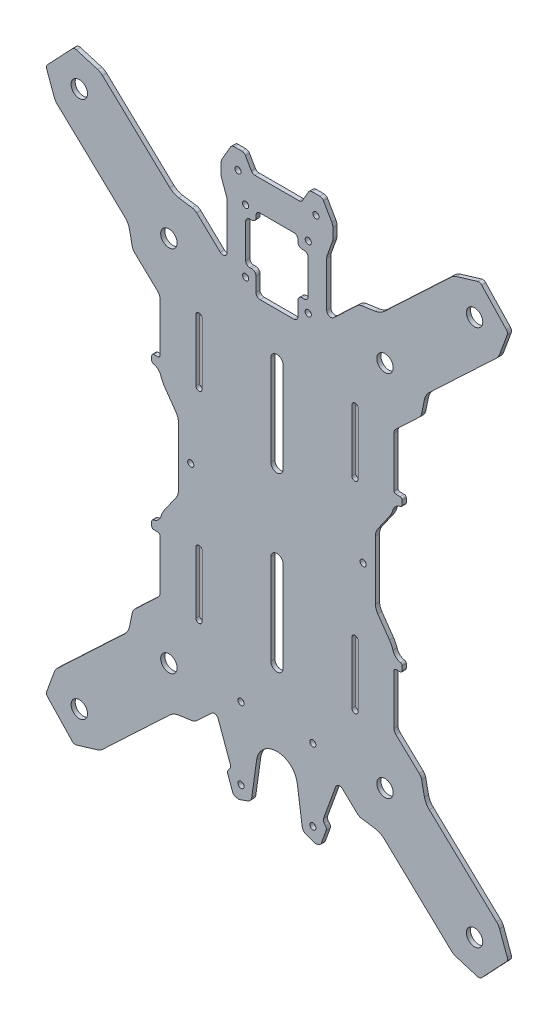
SolidWorks part; units mm, degrees
ref_plane "Front Plane" through (0, 0, 0) normal (0, 0, 1) x (1, 0, 0)
ref_plane "Top Plane" through (0, 0, 0) normal (0, 1, 0) x (1, 0, 0)
ref_plane "Right Plane" through (0, 0, 0) normal (1, 0, 0) x (0, 0, -1)
sketch "Model" plane through (0, 0, 0) normal (0, 0, 1) x (1, 0, 0)
  line L0 (200.4127, 281.3131) -> (207.0194, 282.2803)
  line L1 (211.3501, 284.3765) -> (244.1291, 315.2966)
  line L2 (246.5156, 316.677) -> (256.8221, 319.7815)
  line L3 (270.8811, 306.4885) -> (258.8538, 319.2389)
  line L4 (271.3043, 304.4286) -> (267.604, 294.3207)
  line L5 (266.0868, 292.0187) -> (233.3078, 261.0987)
  line L6 (230.9627, 256.8976) -> (229.6119, 250.3586)
  line L7 (228.4393, 248.258) -> (217.0717, 237.5351)
  line L8 (216.1302, 211.086) -> (216.1302, 235.3528)
  line L9 (219.1302, 210.086) -> (217.1302, 210.086)
  line L10 (220.1302, 206.9971) -> (220.1302, 209.086)
  line L11 (213.96, 199.2031) -> (208.2153, 190.9987)
  line L12 (207.1302, 158.6884) -> (207.1302, 187.5573)
  line L13 (208.2153, 155.2469) -> (213.96, 147.0426)
  line L14 (220.1302, 137.1597) -> (220.1302, 139.2486)
  line L15 (217.1302, 136.1597) -> (219.1302, 136.1597)
  line L16 (216.1302, 110.8929) -> (216.1302, 135.1597)
  line L17 (217.0717, 108.7106) -> (228.4393, 97.9876)
  line L18 (229.6119, 95.8871) -> (230.9627, 89.3481)
  line L19 (233.3078, 85.147) -> (266.0868, 54.2269)
  line L20 (267.604, 51.9249) -> (271.3043, 41.817)
  line L21 (258.8538, 27.0068) -> (270.8811, 39.7571)
  line L22 (256.8221, 26.4641) -> (246.5156, 29.5687)
  line L23 (244.1291, 30.9491) -> (211.3501, 61.8692)
  line L24 (207.0194, 63.9653) -> (200.4127, 64.9325)
  line L25 (198.2474, 65.9806) -> (191.0122, 72.8055)
  line L26 (181.8313, 55.7445) -> (187.7604, 72.0347)
  line L27 (182.1786, 53.7749) -> (182.7352, 53.1115)
  line L28 (183.0825, 51.1419) -> (180.7129, 44.6315)
  line L29 (179.1809, 43.3459) -> (177.8615, 43.1133)
  line L30 (177.3458, 43.1584) -> (173.3678, 44.6063)
  line L31 (171.423, 47.0078) -> (169.0329, 64.0146)
  line L32 (149.2275, 64.0146) -> (146.8374, 47.0078)
  line L33 (144.8926, 44.6063) -> (140.9146, 43.1584)
  line L34 (139.0795, 43.3459) -> (140.3989, 43.1133)
  line L35 (135.1779, 51.1419) -> (137.5474, 44.6315)
  line L36 (136.0818, 53.7749) -> (135.5252, 53.1115)
  line L37 (130.5, 72.0347) -> (136.4291, 55.7445)
  line L38 (120.013, 65.9806) -> (127.2482, 72.8055)
  line L39 (111.241, 63.9653) -> (117.8476, 64.9325)
  line L40 (74.1313, 30.9491) -> (106.9103, 61.8692)
  line L41 (61.4383, 26.4641) -> (71.7448, 29.5687)
  line L42 (47.3793, 39.7571) -> (59.4066, 27.0068)
  line L43 (50.6563, 51.9249) -> (46.9561, 41.817)
  line L44 (84.9526, 85.147) -> (52.1736, 54.2269)
  line L45 (88.6485, 95.8871) -> (87.2977, 89.3481)
  line L46 (101.1887, 108.7106) -> (89.8211, 97.9876)
  line L47 (102.1302, 135.1597) -> (102.1302, 110.8929)
  line L48 (99.1302, 136.1597) -> (101.1302, 136.1597)
  line L49 (98.1302, 139.2486) -> (98.1302, 137.1597)
  line L50 (110.0451, 155.2469) -> (104.3004, 147.0426)
  line L51 (111.1302, 187.5573) -> (111.1302, 158.6884)
  line L52 (104.3004, 199.2031) -> (110.0451, 190.9987)
  line L53 (98.1302, 209.086) -> (98.1302, 206.9971)
  line L54 (101.1302, 210.086) -> (99.1302, 210.086)
  line L55 (102.1302, 235.3528) -> (102.1302, 211.086)
  line L56 (89.8211, 248.258) -> (101.1887, 237.5351)
  line L57 (87.2977, 256.8976) -> (88.6485, 250.3586)
  line L58 (52.1736, 292.0187) -> (84.9526, 261.0987)
  line L59 (46.9561, 304.4286) -> (50.6563, 294.3207)
  line L60 (59.4066, 319.2389) -> (47.3793, 306.4885)
  line L61 (71.7448, 316.677) -> (61.4383, 319.7815)
  line L62 (106.9103, 284.3765) -> (74.1313, 315.2966)
  line L63 (117.8476, 281.3131) -> (111.241, 282.2803)
  line L64 (131.5078, 269.4221) -> (120.013, 280.2651)
  line L65 (134.8802, 292.8447) -> (134.8802, 270.877)
  line L66 (132.1214, 301.1297) -> (134.639, 294.2128)
  line L67 (131.8802, 307.2589) -> (131.8802, 302.4977)
  line L68 (136.499, 316.3307) -> (132.4161, 309.2589)
  line L69 (142.0293, 317.3307) -> (138.231, 317.3307)
  line L70 (146.6481, 311.3307) -> (143.7614, 316.3307)
  line L71 (169.8802, 310.3307) -> (148.3802, 310.3307)
  line L72 (171.6122, 311.3307) -> (174.499, 316.3307)
  line L73 (176.231, 317.3307) -> (180.0293, 317.3307)
  line L74 (181.7614, 316.3307) -> (185.8443, 309.2589)
  line L75 (186.3802, 307.2589) -> (186.3802, 302.4977)
  line L76 (186.139, 301.1297) -> (183.6214, 294.2128)
  line L77 (183.3802, 292.8447) -> (183.3802, 270.877)
  line L78 (186.7526, 269.4221) -> (198.2474, 280.2651)
  line L79 (119.6302, 109.1228) -> (119.6302, 139.1228)
  line L80 (122.6302, 139.1228) -> (122.6302, 109.1228)
  line L81 (198.6302, 237.1228) -> (198.6302, 207.1228)
  line L82 (195.6302, 207.1228) -> (195.6302, 237.1228)
  line L83 (146.8802, 270.1228) -> (145.8802, 270.1228)
  line L84 (148.8802, 261.1228) -> (148.8802, 268.1228)
  line L85 (167.3802, 259.1228) -> (150.8802, 259.1228)
  line L86 (169.3802, 268.1228) -> (169.3802, 261.1228)
  line L87 (172.3802, 270.1228) -> (171.3802, 270.1228)
  line L88 (174.3802, 288.6228) -> (174.3802, 272.1228)
  line L89 (171.3802, 290.6228) -> (172.3802, 290.6228)
  line L90 (169.3802, 293.6228) -> (169.3802, 292.6228)
  line L91 (150.8802, 295.6228) -> (167.3802, 295.6228)
  line L92 (148.8802, 292.6228) -> (148.8802, 293.6228)
  line L93 (145.8802, 290.6228) -> (146.8802, 290.6228)
  line L94 (143.8802, 272.1228) -> (143.8802, 288.6228)
  line L95 (162.1302, 237.1228) -> (162.1302, 193.1228)
  line L96 (156.1302, 193.1228) -> (156.1302, 237.1228)
  line L97 (156.1302, 109.1228) -> (156.1302, 153.1228)
  line L98 (162.1302, 153.1228) -> (162.1302, 109.1228)
  line L99 (122.6302, 237.1228) -> (122.6302, 207.1228)
  line L100 (119.6302, 207.1228) -> (119.6302, 237.1228)
  line L101 (195.6302, 109.1228) -> (195.6302, 139.1228)
  line L102 (198.6302, 139.1228) -> (198.6302, 109.1228)
  arc A0 (200.4127, 281.3131) -> (198.2474, 280.2651) centre (200.9921, 277.3553) ccw
  arc A1 (207.0194, 282.2803) -> (211.3501, 284.3765) centre (205.8606, 290.1959) ccw
  arc A2 (246.5156, 316.677) -> (244.1291, 315.2966) centre (248.2461, 310.932) ccw
  arc A3 (258.8538, 319.2389) -> (256.8221, 319.7815) centre (257.399, 317.8665) ccw
  arc A4 (271.3043, 304.4286) -> (270.8811, 306.4885) centre (269.4262, 305.1162) ccw
  arc A5 (266.0868, 292.0187) -> (267.604, 294.3207) centre (261.9697, 296.3833) ccw
  arc A6 (233.3078, 261.0987) -> (230.9627, 256.8976) centre (238.7973, 255.2792) ccw
  arc A7 (228.4393, 248.258) -> (229.6119, 250.3586) centre (225.6946, 251.1678) ccw
  arc A8 (217.0717, 237.5351) -> (216.1302, 235.3528) centre (219.1302, 235.3528) ccw
  arc A9 (216.1302, 211.086) -> (217.1302, 210.086) centre (217.1302, 211.086) ccw
  arc A10 (220.1302, 209.086) -> (219.1302, 210.086) centre (219.1302, 209.086) ccw
  arc A11 (219.3067, 206.0128) -> (220.1302, 206.9971) centre (219.1302, 206.9971) ccw
  arc A12 (219.3067, 206.0128) -> (215.6502, 202.726) centre (220.1302, 201.4193) ccw
  arc A13 (213.96, 199.2031) -> (215.6502, 202.726) centre (204.1302, 206.086) ccw
  arc A14 (208.2153, 190.9987) -> (207.1302, 187.5573) centre (213.1302, 187.5573) ccw
  arc A15 (207.1302, 158.6884) -> (208.2153, 155.2469) centre (213.1302, 158.6884) ccw
  arc A16 (215.6502, 143.5197) -> (213.96, 147.0426) centre (204.1302, 140.1597) ccw
  arc A17 (215.6502, 143.5197) -> (219.3067, 140.2329) centre (220.1302, 144.8263) ccw
  arc A18 (220.1302, 139.2486) -> (219.3067, 140.2329) centre (219.1302, 139.2486) ccw
  arc A19 (219.1302, 136.1597) -> (220.1302, 137.1597) centre (219.1302, 137.1597) ccw
  arc A20 (217.1302, 136.1597) -> (216.1302, 135.1597) centre (217.1302, 135.1597) ccw
  arc A21 (216.1302, 110.8929) -> (217.0717, 108.7106) centre (219.1302, 110.8929) ccw
  arc A22 (229.6119, 95.8871) -> (228.4393, 97.9876) centre (225.6946, 95.0779) ccw
  arc A23 (230.9627, 89.3481) -> (233.3078, 85.147) centre (238.7973, 90.9665) ccw
  arc A24 (267.604, 51.9249) -> (266.0868, 54.2269) centre (261.9697, 49.8623) ccw
  arc A25 (270.8811, 39.7571) -> (271.3043, 41.817) centre (269.4262, 41.1295) ccw
  arc A26 (256.8221, 26.4641) -> (258.8538, 27.0068) centre (257.399, 28.3791) ccw
  arc A27 (244.1291, 30.9491) -> (246.5156, 29.5687) centre (248.2461, 35.3137) ccw
  arc A28 (211.3501, 61.8692) -> (207.0194, 63.9653) centre (205.8606, 56.0497) ccw
  arc A29 (198.2474, 65.9806) -> (200.4127, 64.9325) centre (200.9921, 68.8903) ccw
  arc A30 (191.0122, 72.8055) -> (187.7604, 72.0347) centre (189.6398, 71.3507) ccw
  arc A31 (181.8313, 55.7445) -> (182.1786, 53.7749) centre (183.7106, 55.0605) ccw
  arc A32 (183.0825, 51.1419) -> (182.7352, 53.1115) centre (181.2031, 51.8259) ccw
  arc A33 (179.1809, 43.3459) -> (180.7129, 44.6315) centre (178.8336, 45.3155) ccw
  arc A34 (177.3458, 43.1584) -> (177.8615, 43.1133) centre (177.6878, 44.0981) ccw
  arc A35 (171.423, 47.0078) -> (173.3678, 44.6063) centre (174.3938, 47.4253) ccw
  arc A36 (169.0329, 64.0146) -> (149.2275, 64.0146) centre (159.1302, 62.6228) ccw
  arc A37 (144.8926, 44.6063) -> (146.8374, 47.0078) centre (143.8666, 47.4253) ccw
  arc A38 (140.3989, 43.1133) -> (140.9146, 43.1584) centre (140.5726, 44.0981) ccw
  arc A39 (137.5474, 44.6315) -> (139.0795, 43.3459) centre (139.4268, 45.3155) ccw
  arc A40 (135.5252, 53.1115) -> (135.1779, 51.1419) centre (137.0572, 51.8259) ccw
  arc A41 (136.0818, 53.7749) -> (136.4291, 55.7445) centre (134.5497, 55.0605) ccw
  arc A42 (130.5, 72.0347) -> (127.2482, 72.8055) centre (128.6206, 71.3507) ccw
  arc A43 (117.8476, 64.9325) -> (120.013, 65.9806) centre (117.2683, 68.8903) ccw
  arc A44 (111.241, 63.9653) -> (106.9103, 61.8692) centre (112.3997, 56.0497) ccw
  arc A45 (71.7448, 29.5687) -> (74.1313, 30.9491) centre (70.0143, 35.3137) ccw
  arc A46 (59.4066, 27.0068) -> (61.4383, 26.4641) centre (60.8614, 28.3791) ccw
  arc A47 (46.9561, 41.817) -> (47.3793, 39.7571) centre (48.8342, 41.1295) ccw
  arc A48 (52.1736, 54.2269) -> (50.6563, 51.9249) centre (56.2907, 49.8623) ccw
  arc A49 (84.9526, 85.147) -> (87.2977, 89.3481) centre (79.4631, 90.9665) ccw
  arc A50 (89.8211, 97.9876) -> (88.6485, 95.8871) centre (92.5658, 95.0779) ccw
  arc A51 (101.1887, 108.7106) -> (102.1302, 110.8929) centre (99.1302, 110.8929) ccw
  arc A52 (102.1302, 135.1597) -> (101.1302, 136.1597) centre (101.1302, 135.1597) ccw
  arc A53 (98.1302, 137.1597) -> (99.1302, 136.1597) centre (99.1302, 137.1597) ccw
  arc A54 (98.9537, 140.2329) -> (98.1302, 139.2486) centre (99.1302, 139.2486) ccw
  arc A55 (98.9537, 140.2329) -> (102.6102, 143.5197) centre (98.1302, 144.8263) ccw
  arc A56 (104.3004, 147.0426) -> (102.6102, 143.5197) centre (114.1302, 140.1597) ccw
  arc A57 (110.0451, 155.2469) -> (111.1302, 158.6884) centre (105.1302, 158.6884) ccw
  arc A58 (111.1302, 187.5573) -> (110.0451, 190.9987) centre (105.1302, 187.5573) ccw
  arc A59 (102.6102, 202.726) -> (104.3004, 199.2031) centre (114.1302, 206.086) ccw
  arc A60 (102.6102, 202.726) -> (98.9537, 206.0128) centre (98.1302, 201.4193) ccw
  arc A61 (98.1302, 206.9971) -> (98.9537, 206.0128) centre (99.1302, 206.9971) ccw
  arc A62 (99.1302, 210.086) -> (98.1302, 209.086) centre (99.1302, 209.086) ccw
  arc A63 (101.1302, 210.086) -> (102.1302, 211.086) centre (101.1302, 211.086) ccw
  arc A64 (102.1302, 235.3528) -> (101.1887, 237.5351) centre (99.1302, 235.3528) ccw
  arc A65 (88.6485, 250.3586) -> (89.8211, 248.258) centre (92.5658, 251.1678) ccw
  arc A66 (87.2977, 256.8976) -> (84.9526, 261.0987) centre (79.4631, 255.2792) ccw
  arc A67 (50.6563, 294.3207) -> (52.1736, 292.0187) centre (56.2907, 296.3833) ccw
  arc A68 (47.3793, 306.4885) -> (46.9561, 304.4286) centre (48.8342, 305.1162) ccw
  arc A69 (61.4383, 319.7815) -> (59.4066, 319.2389) centre (60.8614, 317.8665) ccw
  arc A70 (74.1313, 315.2966) -> (71.7448, 316.677) centre (70.0143, 310.932) ccw
  arc A71 (106.9103, 284.3765) -> (111.241, 282.2803) centre (112.3997, 290.1959) ccw
  arc A72 (120.013, 280.2651) -> (117.8476, 281.3131) centre (117.2683, 277.3553) ccw
  arc A73 (131.5078, 269.4221) -> (134.8802, 270.877) centre (132.8802, 270.8769) ccw
  arc A74 (134.8802, 292.8447) -> (134.639, 294.2128) centre (130.8802, 292.8447) ccw
  arc A75 (131.8802, 302.4977) -> (132.1214, 301.1297) centre (135.8802, 302.4977) ccw
  arc A76 (132.4161, 309.2589) -> (131.8802, 307.2589) centre (135.8802, 307.2589) ccw
  arc A77 (138.231, 317.3307) -> (136.499, 316.3307) centre (138.231, 315.3307) ccw
  arc A78 (143.7614, 316.3307) -> (142.0293, 317.3307) centre (142.0293, 315.3307) ccw
  arc A79 (146.6481, 311.3307) -> (148.3802, 310.3307) centre (148.3802, 312.3307) ccw
  arc A80 (169.8802, 310.3307) -> (171.6122, 311.3307) centre (169.8802, 312.3307) ccw
  arc A81 (176.231, 317.3307) -> (174.499, 316.3307) centre (176.231, 315.3307) ccw
  arc A82 (181.7614, 316.3307) -> (180.0293, 317.3307) centre (180.0293, 315.3307) ccw
  arc A83 (186.3802, 307.2589) -> (185.8443, 309.2589) centre (182.3802, 307.2589) ccw
  arc A84 (186.139, 301.1297) -> (186.3802, 302.4977) centre (182.3802, 302.4977) ccw
  arc A85 (183.6214, 294.2128) -> (183.3802, 292.8447) centre (187.3802, 292.8447) ccw
  arc A86 (183.3802, 270.877) -> (186.7526, 269.4221) centre (185.3802, 270.8769) ccw
  arc A87 (122.6302, 139.1228) -> (119.6302, 139.1228) centre (121.1302, 139.1228) ccw
  arc A88 (119.6302, 109.1228) -> (122.6302, 109.1228) centre (121.1302, 109.1228) ccw
  arc A89 (195.6302, 207.1228) -> (198.6302, 207.1228) centre (197.1302, 207.1228) ccw
  arc A90 (198.6302, 237.1228) -> (195.6302, 237.1228) centre (197.1302, 237.1228) ccw
  arc A91 (143.8802, 272.1228) -> (145.8802, 270.1228) centre (145.8802, 272.1228) ccw
  arc A92 (148.8802, 268.1228) -> (146.8802, 270.1228) centre (146.8802, 268.1228) ccw
  arc A93 (148.8802, 261.1228) -> (150.8802, 259.1228) centre (150.8802, 261.1228) ccw
  arc A94 (167.3802, 259.1228) -> (169.3802, 261.1228) centre (167.3802, 261.1228) ccw
  arc A95 (171.3802, 270.1228) -> (169.3802, 268.1228) centre (171.3802, 268.1228) ccw
  arc A96 (172.3802, 270.1228) -> (174.3802, 272.1228) centre (172.3802, 272.1228) ccw
  arc A97 (174.3802, 288.6228) -> (172.3802, 290.6228) centre (172.3802, 288.6228) ccw
  arc A98 (169.3802, 292.6228) -> (171.3802, 290.6228) centre (171.3802, 292.6228) ccw
  arc A99 (169.3802, 293.6228) -> (167.3802, 295.6228) centre (167.3802, 293.6228) ccw
  arc A100 (150.8802, 295.6228) -> (148.8802, 293.6228) centre (150.8802, 293.6228) ccw
  arc A101 (146.8802, 290.6228) -> (148.8802, 292.6228) centre (146.8802, 292.6228) ccw
  arc A102 (145.8802, 290.6228) -> (143.8802, 288.6228) centre (145.8802, 288.6228) ccw
  circle A103 centre (174.3802, 265.1228) radius 1.5
  circle A104 centre (143.8802, 295.6228) radius 1.5
  circle A105 centre (176.6302, 84.7678) radius 1.5
  arc A106 (156.1302, 193.1228) -> (162.1302, 193.1228) centre (159.1302, 193.1228) ccw
  arc A107 (162.1302, 237.1228) -> (156.1302, 237.1228) centre (159.1302, 237.1228) ccw
  circle A108 centre (141.6302, 49.7678) radius 1.5
  circle A109 centre (106.4955, 262.7726) radius 4
  circle A110 centre (62.8496, 303.9434) radius 4
  circle A111 centre (106.4955, 83.4731) radius 4
  circle A112 centre (62.8496, 42.3023) radius 4
  circle A113 centre (255.4108, 42.3023) radius 4
  circle A114 centre (211.7649, 83.4731) radius 4
  circle A115 centre (255.4108, 303.9434) radius 4
  circle A116 centre (211.7649, 262.7726) radius 4
  circle A117 centre (176.6302, 49.7678) radius 1.5
  arc A118 (162.1302, 153.1228) -> (156.1302, 153.1228) centre (159.1302, 153.1228) ccw
  arc A119 (156.1302, 109.1228) -> (162.1302, 109.1228) centre (159.1302, 109.1228) ccw
  circle A120 centre (141.6302, 84.7678) radius 1.5
  circle A121 centre (174.3802, 295.6228) radius 1.5
  circle A122 centre (143.8802, 265.1228) radius 1.5
  circle A123 centre (140.1302, 308.3307) radius 3.5 construction
  circle A124 centre (178.1302, 308.3307) radius 3.5 construction
  circle A125 centre (117.1302, 173.1228) radius 3.5 construction
  circle A126 centre (201.1302, 173.1228) radius 3.5 construction
  arc A127 (119.6302, 207.1228) -> (122.6302, 207.1228) centre (121.1302, 207.1228) ccw
  arc A128 (122.6302, 237.1228) -> (119.6302, 237.1228) centre (121.1302, 237.1228) ccw
  arc A129 (198.6302, 139.1228) -> (195.6302, 139.1228) centre (197.1302, 139.1228) ccw
  arc A130 (195.6302, 109.1228) -> (198.6302, 109.1228) centre (197.1302, 109.1228) ccw
  circle A131 centre (201.1302, 173.1228) radius 1.5
  circle A132 centre (117.1302, 173.1228) radius 1.5
  circle A133 centre (178.1302, 308.3307) radius 1.5
  circle A134 centre (140.1302, 308.3307) radius 1.5
extrude "Boss-Extrude1" add sketch "Model" along normal blind 2
